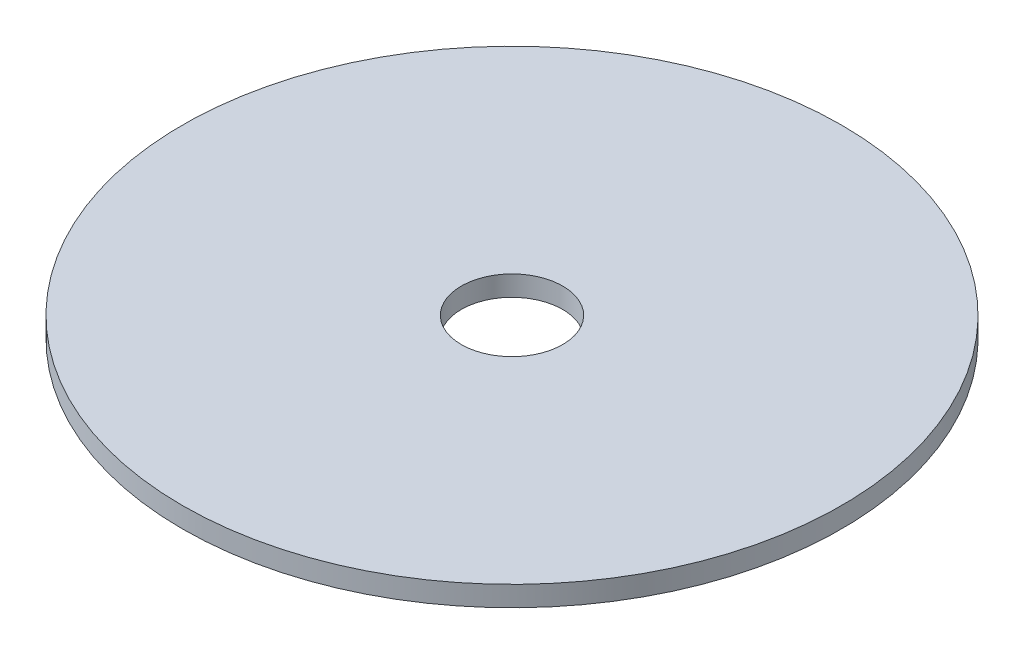
SolidWorks part; units mm, degrees
ref_plane "Front Plane" through (0, 0, 0) normal (0, 0, 1) x (1, 0, 0)
ref_plane "Top Plane" through (0, 0, 0) normal (0, 1, 0) x (1, 0, 0)
ref_plane "Right Plane" through (0, 0, 0) normal (1, 0, 0) x (0, 0, -1)
sketch "Sketch1" plane through (0, 0, 0) normal (0, 1, 0) x (1, 0, 0)
  circle A0 centre (0, 0) radius 65
  dimension "D1" = 130
extrude "Boss-Extrude1" add sketch "Sketch1" along normal blind 4
sketch "Sketch2" plane through (0, 4, 0) normal (0, 1, 0) x (1, 0, 0)
  circle A0 centre (0, 0) radius 10
  dimension "D1" = 20
extrude "Cut-Extrude1" cut sketch "Sketch2" against normal blind 10
